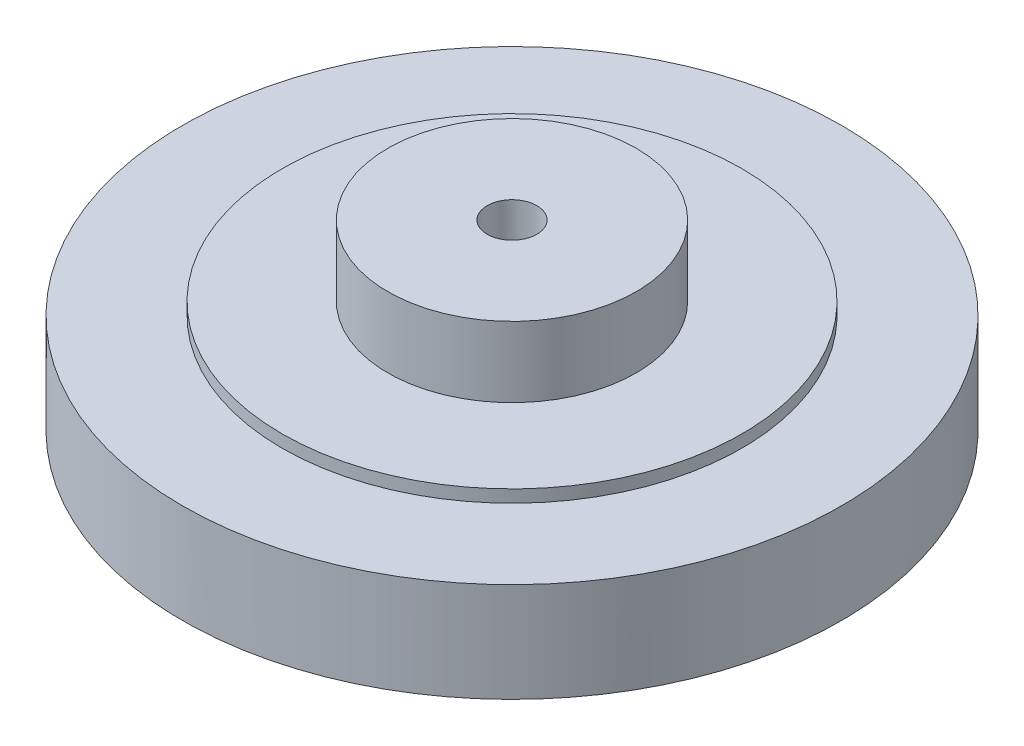
SolidWorks part; units mm, degrees
material "6061 Alloy"
ref_plane "Front Plane" through (0, 0, 0) normal (0, 0, 1) x (1, 0, 0)
ref_plane "Top Plane" through (0, 0, 0) normal (0, 1, 0) x (1, 0, 0)
ref_plane "Right Plane" through (0, 0, 0) normal (1, 0, 0) x (0, 0, -1)
sketch "Sketch1" plane through (0, 0, 0) normal (0, 0, 1) x (1, 0, 0)
  line L0 (0, 0) -> (0, 22) construction
  line L1 (0, 22) -> (3, 22) construction
  line L2 (0, 0) -> (3, 0) construction
  line L3 (3, 22) -> (3, 0)
  line L4 (3, 22) -> (15, 22)
  line L5 (15, 22) -> (15, 12)
  line L6 (15, 12) -> (27.75, 12)
  line L7 (27.75, 12) -> (27.75, 0)
  line L8 (27.75, 0) -> (3, 0)
  dimension "D1" = 30
  dimension "D2" = 10
  dimension "D3" = 6
  dimension "D4" = 55.5
  dimension "D5" = 12
revolve "Revolve1" add sketch "Sketch1" angle 360 about L0
sketch "Sketch2" plane through (0, 0, 0) normal (0, -1, 0) x (1, 0, 0)
  circle A0 centre (0, 0) radius 39.7887
  circle A1 centre (0, 0) radius 27.75 construction
  circle A2 centre (0, 0) radius 27.75
  dimension "D1" = 79.5775
extrude "Boss-Extrude1" add sketch "Sketch2" against normal up to surface (12 mm away) separate body up to face at (0, 12, -15)
sketch "Sketch3" plane through (0, 0, 0) normal (0, -1, 0) x (1, 0, 0)
  circle A2 centre (0, 0) radius 3 construction
  circle A3 centre (0, 0) radius 27.75 construction
  circle A4 centre (0, 0) radius 3
  circle A5 centre (0, 0) radius 27.75
extrude "Boss-Extrude2" add sketch "Sketch3" against normal blind 15 from offset 1.5
